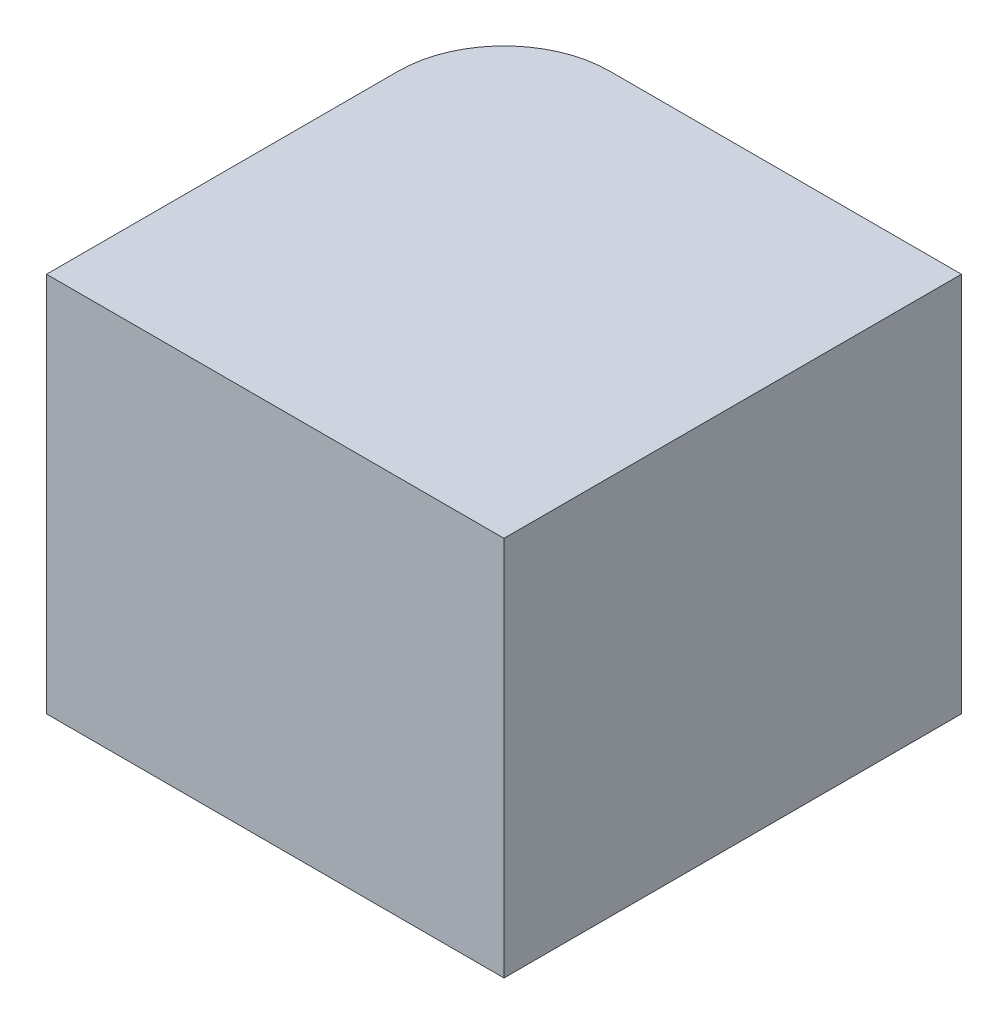
SolidWorks part; units mm, degrees
ref_plane "Front Plane" through (0, 0, 0) normal (0, 0, 1) x (1, 0, 0)
ref_plane "Top Plane" through (0, 0, 0) normal (0, 1, 0) x (1, 0, 0)
ref_plane "Right Plane" through (0, 0, 0) normal (1, 0, 0) x (0, 0, -1)
sketch "Sketch2" plane through (0, 0, 0) normal (0, 1, 0) x (1, 0, 0)
  line L0 (0, 0) -> (0, 8.65)
  line L1 (0, 8.65) -> (8.65, 8.65)
  line L2 (8.65, 8.65) -> (8.65, 0)
  line L3 (8.65, 0) -> (0, 0)
  dimension "D1" = 8.65
  dimension "D2" = 8.65
extrude "Boss-Extrude1" add sketch "Sketch2" along normal blind 7.2
fillet "Fillet1" radius 2 1 edges at (0, 3.6, -8.65)
